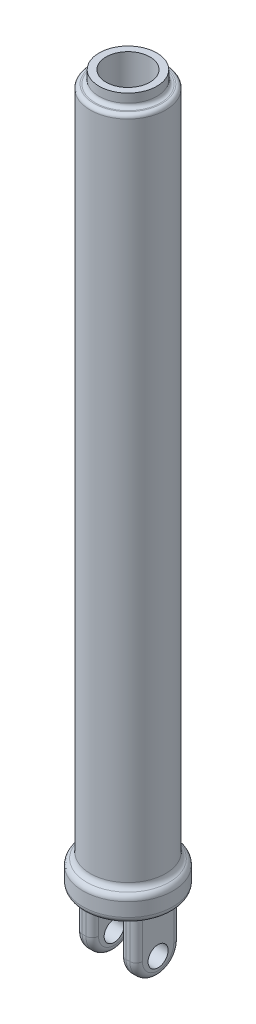
SolidWorks part; units mm, degrees
material "Plain Carbon Steel"
ref_plane "Front" through (0, 0, 0) normal (0, 0, 1) x (1, 0, 0)
ref_plane "Top" through (0, 0, 0) normal (0, 1, 0) x (1, 0, 0)
ref_plane "Right" through (0, 0, 0) normal (1, 0, 0) x (0, 0, -1)
sketch "Sketch1" plane through (0, 0, 0) normal (0, 0, 1) x (1, 0, 0)
  line L0 (0, 0) -> (0, 585) construction
  line L1 (-30, 552) -> (-30, 24.9774)
  line L2 (0, 565) -> (-23, 565) construction
  line L3 (0, 0) -> (-30.8239, 0)
  line L4 (-35.8239, 15.8911) -> (-35.8239, 5)
  line L5 (-27, 555) -> (-26, 555)
  line L6 (-23, 558) -> (-23, 565)
  line L7 (-17.5, 565) -> (-17.5, 40)
  line L8 (-17.5, 40) -> (0, 40)
  line L9 (-17.5, 565) -> (-23, 565)
  line L10 (0, 40) -> (0, 0)
  arc A1 (-30, 24.9774) -> (-32.9119, 20.4342) centre (-35, 24.9774) cw
  arc A2 (-35.8239, 15.8911) -> (-32.9119, 20.4342) centre (-30.8239, 15.8911) cw
  arc A3 (-30.8239, 0) -> (-35.8239, 5) centre (-30.8239, 5) cw
  arc A4 (-30, 552) -> (-27, 555) centre (-27, 552) cw
  arc A5 (-26, 555) -> (-23, 558) centre (-26, 558) ccw
  dimension "D2" = 5
  dimension "D3" = 5
  dimension "D5" = 3
  dimension "D8" = 565
  dimension "D1" = 585
  dimension "D4" = 30
  dimension "D6" = 10
  dimension "D7" = 1
  dimension "D9" = 525
  dimension "D10" = 35
revolve "Revolve1" add sketch "Sketch1" angle 360 about L10
sketch "Sketch2" plane through (0, 0, 0) normal (0, -1, 0) x (1, 0, 0)
  line L0 (0, 0) -> (0, 30.8239) construction
  line L1 (0, 0) -> (30.8239, 0) construction
  line L2 (-11, -17.5) -> (-24, 17.5) construction
  line L3 (11, 17.5) -> (24, 17.5)
  line L4 (11, 17.5) -> (11, -17.5)
  line L5 (11, -17.5) -> (24, -17.5)
  line L6 (24, 17.5) -> (24, -17.5)
  line L7 (11, 17.5) -> (24, -17.5) construction
  line L8 (11, -17.5) -> (24, 17.5) construction
  line L9 (-11, 17.5) -> (-24, -17.5) construction
  line L10 (-24, 17.5) -> (-24, -17.5)
  line L11 (-11, -17.5) -> (-24, -17.5)
  line L12 (-11, 17.5) -> (-11, -17.5)
  line L13 (-11, 17.5) -> (-24, 17.5)
  circle A0 centre (0, 0) radius 30.8239 construction
  point P6 (17.5, 0)
  point P16 (-17.5, 0)
  dimension "D1" = 35
  dimension "D2" = 48
  dimension "D3" = 22
extrude "Boss-Extrude1" add sketch "Sketch2" along normal blind 50
sketch "Sketch3" plane through (24, 0, 0) normal (1, 0, 0) x (0, 0, -1)
  line L0 (-17.5, -32.5) -> (-17.5, -50)
  line L1 (-17.5, -50) -> (17.5, -50)
  line L2 (17.5, -50) -> (17.5, -32.5)
  line L3 (-30.8239, 0) -> (30.8239, 0) construction
  arc A0 (-17.5, -32.5) -> (17.5, -32.5) centre (0, -32.5) ccw
  circle A2 centre (0, -35) radius 8
  dimension "D1" = 16
  dimension "D2" = 35
extrude "Cut-Extrude1" cut sketch "Sketch3" against normal through all
fillet "Fillet1" radius 5 12 edges at (24, -16.25, 17.5) (24, -16.25, -17.5) (11, -16.25, 17.5) (11, -16.25, -17.5) (-11, -16.25, -17.5) (-11, -16.25, 17.5) (-24, -16.25, 17.5) (-24, -16.25, -17.5) (24, -50, 0) (11, -50, 0) (-11, -50, 0) (-24, -50, 0)
ref_point "Point1"
